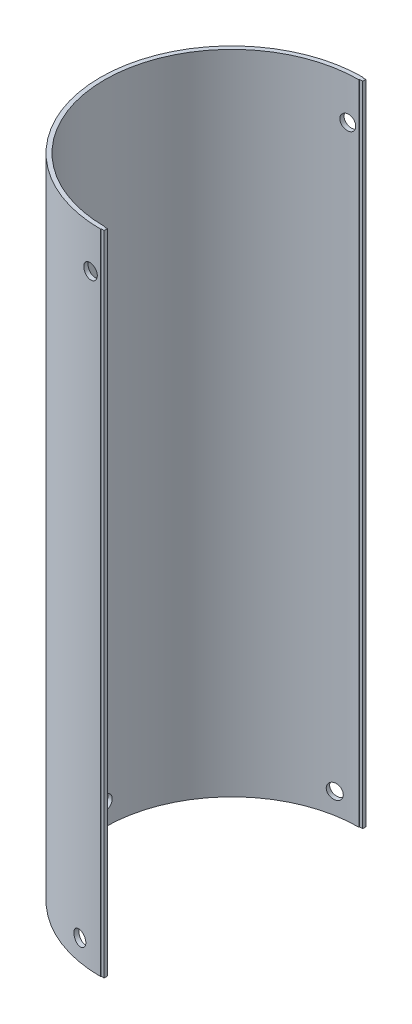
SolidWorks part; units mm, degrees
material "ABS"
ref_plane "Front Plane" through (0, 0, 0) normal (0, 0, 1) x (1, 0, 0)
ref_plane "Top Plane" through (0, 0, 0) normal (0, 1, 0) x (1, 0, 0)
ref_plane "Right Plane" through (0, 0, 0) normal (1, 0, 0) x (0, 0, -1)
sketch "Sketch3" plane through (0, 0, 0) normal (0, 1, 0) x (1, 0, 0)
  line L0 (0, -60.49) -> (0, -60.75)
  line L1 (0, -60.75) -> (1.5, -60.75)
  line L2 (1.5, -60.75) -> (1.5, -62.25)
  line L3 (1.5, -62.25) -> (0, -62.25)
  line L4 (0, -62.25) -> (0, -62.5)
  line L5 (-35.2, 0) -> (35.2, 0) construction
  line L6 (0, 62.25) -> (0, 62.5)
  line L7 (0, 60.49) -> (0, 60.75)
  line L8 (0, 60.75) -> (1.5, 60.75)
  line L9 (1.5, 62.25) -> (0, 62.25)
  line L10 (1.5, 60.75) -> (1.5, 62.25)
  arc A0 (0, 62.5) -> (0, -62.5) centre (0, 0) ccw
  arc A1 (0, 60.49) -> (0, -60.49) centre (0, 0) ccw
  dimension "D1" = 62.5
  dimension "D2" = 2.01
  dimension "D3" = 1.5
  dimension "D4" = 0.25
  dimension "D5" = 0.26
  dimension "D6" = 1.5
extrude "Boss-Extrude1" add sketch "Sketch3" along normal blind 308 contours A1 L0 L1 L2 L3 L4 A0 L6 L9 L10 L8 L7
sketch "Sketch4" plane through (0, 0, 0) normal (1, 0, 0) x (0, 0, -1)
  circle A0 centre (0, 10) radius 3.5
  dimension "D1" = 7
  dimension "D2" = 10
extrude "Cut-Extrude1" cut sketch "Sketch4" against normal up to next
pattern_circular "CirPattern2" count 2 over 80 about axis through (0, 0, 0) along (0, 1, 0) of "Cut-Extrude1"
mirror "Mirror1" about plane through (0, 0, 0) normal (0, 0, 1) of "CirPattern2"
ref_plane "Plane1" through (0, 0, -62.5) normal (0, 0, -1) x (-1, 0, 0)
sketch "Sketch5" plane through (0, 0, -62.5) normal (0, 0, -1) x (-1, 0, 0)
  line L0 (62.5, 308) -> (0, 308) construction
  line L1 (0, 308) -> (0, 0) construction
  circle A0 centre (5, 288) radius 3.5
  dimension "D1" = 7
  dimension "D2" = 20
  dimension "D3" = 5
extrude "Cut-Extrude2" cut sketch "Sketch5" against normal mid plane 10 contours A0
mirror "Mirror2" about plane through (0, 0, 0) normal (0, 0, 1) of "Cut-Extrude2"
